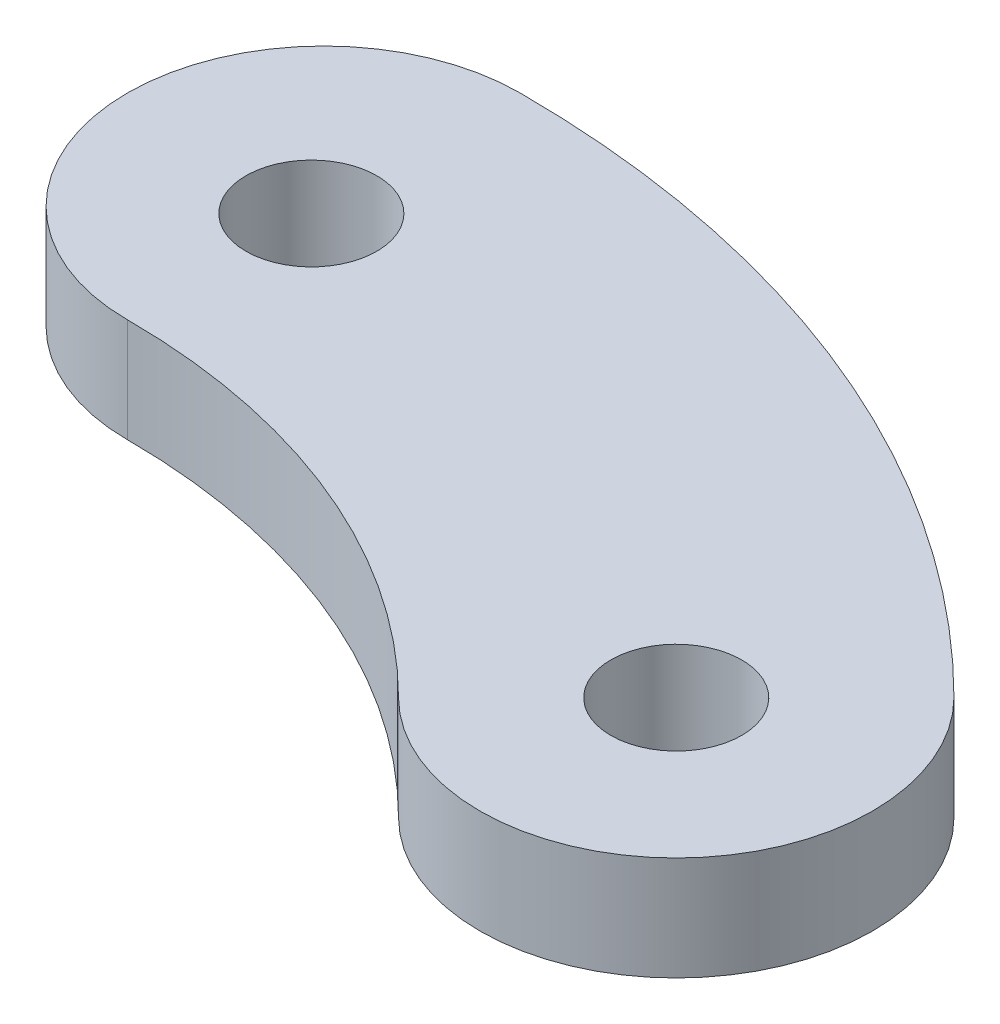
SolidWorks part; units mm, degrees
ref_plane "Front Plane" through (0, 0, 0) normal (0, 0, 1) x (1, 0, 0)
ref_plane "Top Plane" through (0, 0, 0) normal (0, 1, 0) x (1, 0, 0)
ref_plane "Right Plane" through (0, 0, 0) normal (1, 0, 0) x (0, 0, -1)
sketch "Sketch1" plane through (0, 0, 0) normal (0, 1, 0) x (1, 0, 0)
  line L0 (0, 65) -> (0, 0) construction
  line L1 (0, 0) -> (45.9619, 45.9619) construction
  arc A0 (0, 65) -> (45.9619, 45.9619) centre (0, 0) cw construction
  arc A1 (56.5685, 56.5685) -> (0, 80) centre (0, 0) ccw
  arc A2 (35.3553, 35.3553) -> (0, 50) centre (0, 0) ccw
  arc A3 (35.3553, 35.3553) -> (56.5685, 56.5685) centre (45.9619, 45.9619) ccw
  arc A4 (0, 80) -> (0, 50) centre (0, 65) ccw
  circle A5 centre (0, 64.0538) radius 5
  circle A6 centre (45.9619, 45.9619) radius 5
  point P4 (24.8744, 60.0522)
  dimension "D2" = 50
  dimension "D3" = 80
  dimension "D1" = 45
extrude "Boss-Extrude1" add sketch "Sketch1" along normal blind 7.9375
